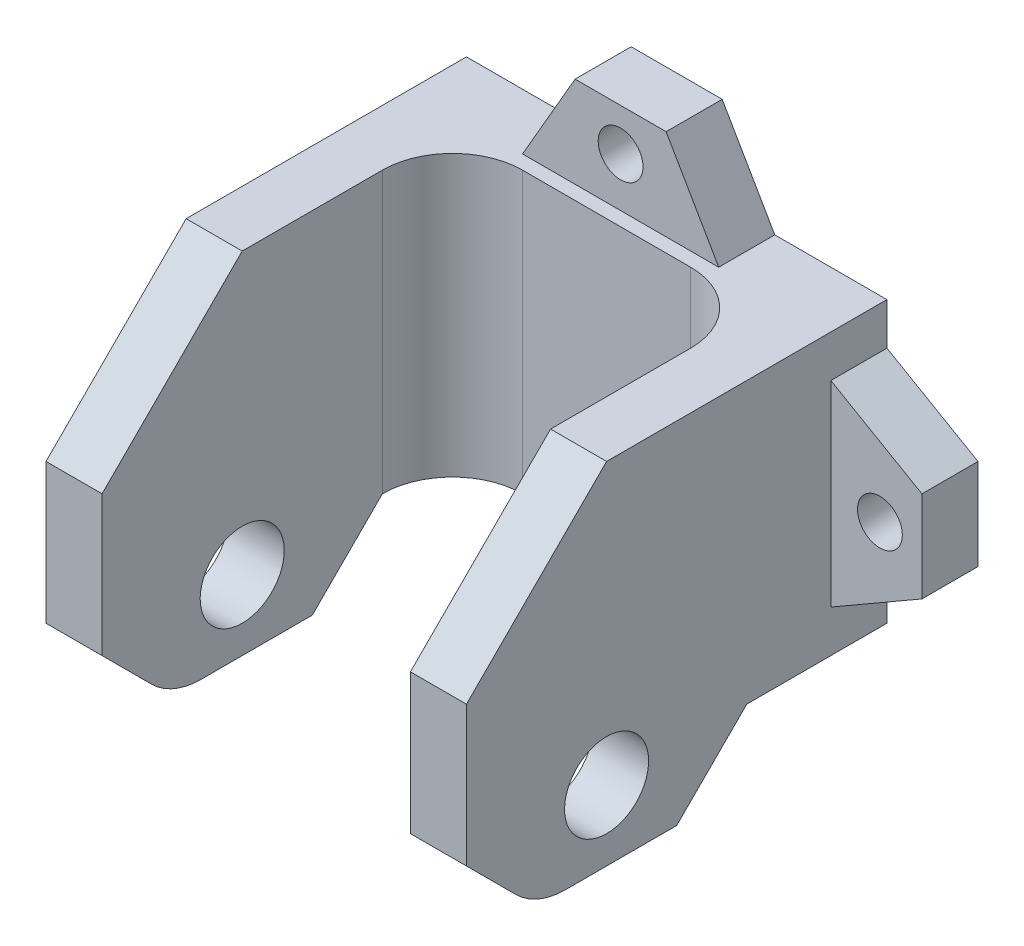
SolidWorks part; units mm, degrees
ref_plane "前视基准面" through (0, 0, 0) normal (0, 0, 1) x (1, 0, 0)
ref_plane "上视基准面" through (0, 0, 0) normal (0, 1, 0) x (1, 0, 0)
ref_plane "右视基准面" through (0, 0, 0) normal (1, 0, 0) x (0, 0, -1)
sketch "Sketch1" plane through (0, 0, 0) normal (0, 0, 1) x (1, 0, 0)
  line L0 (0, 285) -> (0, -299.6017) construction
  line L1 (-15, -45) -> (15, -45)
  line L2 (-15, -45) -> (-15, -85)
  line L3 (-15, -85) -> (15, -85)
  line L4 (15, -45) -> (15, -85)
  line L5 (225, 285) -> (-225, 285) construction
  line L6 (-115, -285) -> (115, -285) construction
  point P9 (0, -45)
  dimension "D1" = 30
  dimension "D2" = 40
  dimension "D3" = 200
extrude "Boss-Extrude1" add sketch "Sketch1" along normal blind 5
sketch "Sketch2" plane through (0, 0, 5) normal (0, 0, 1) x (1, 0, 0)
  line L0 (-15, -85) -> (15, -85) construction
  line L1 (-15, -45) -> (-11, -45)
  line L2 (-15, -45) -> (-15, -85)
  line L3 (-15, -85) -> (-11, -85)
  line L4 (-11, -45) -> (-11, -85)
  line L6 (15, -45) -> (11, -45)
  line L7 (15, -45) -> (15, -85)
  line L8 (15, -85) -> (11, -85)
  line L9 (11, -45) -> (11, -85)
  dimension "D1" = 4
  dimension "D2" = 4
extrude "Boss-Extrude2" add sketch "Sketch2" along normal blind 25
chamfer "Chamfer1" distance 10 angle 45 4 edges at (13, -85, 30) (-13, -85, 30) (13, -45, 30) (-13, -45, 30)
sketch "Sketch3" plane through (-15, 0, 0) normal (-1, 0, 0) x (0, 0, 1)
  line L0 (20, -45) -> (0, -45) construction
  line L1 (30, -55) -> (30, -75) construction
  circle A0 centre (20, -65) radius 3
  dimension "D1" = 20
  dimension "D2" = 6
  dimension "D3" = 10
extrude "Cut-Extrude1" cut sketch "Sketch3" against normal blind 76
sketch "Sketch4" plane through (-15, 0, 0) normal (-1, 0, 0) x (0, 0, 1)
  line L0 (30, -70) -> (15, -70)
  line L1 (30, -55) -> (30, -75) construction
  line L2 (15, -70) -> (10, -65)
  line L3 (10, -65) -> (0, -65)
  line L4 (0, -45) -> (0, -85) construction
  line L5 (30, -70) -> (31.2179, -87.2551)
  line L6 (31.2179, -87.2551) -> (-4.9062, -89.8049)
  line L7 (-4.9062, -89.8049) -> (0, -65)
  line L8 (20, -45) -> (5, -45) construction
  dimension "D1" = 25
  dimension "D2" = 5
  dimension "D3" = 45
  dimension "D4" = 10
extrude "Cut-Extrude2" cut sketch "Sketch4" against normal blind 76
chamfer "Chamfer2" distance 5 angle 45 2 edges at (-13, -70, 30) (13, -70, 30)
fillet "Fillet1" radius 5 2 edges at (11, -55, 5) (-11, -55, 5)
fillet "Fillet2" radius 5 2 edges at (13, -70, 25) (-13, -70, 25)
sketch "Sketch5" plane through (0, 0, 0) normal (0, 0, -1) x (-1, 0, 0)
  line L0 (7, -45) -> (3.2472, -38.5)
  line L1 (11, -45) -> (6, -45) construction
  line L2 (3.2472, -38.5) -> (-3.2472, -38.5)
  line L3 (-3.2472, -38.5) -> (-7, -45)
  line L4 (-6, -45) -> (-11, -45) construction
  line L5 (-7, -45) -> (7, -45)
  line L6 (15, -48) -> (21.5, -51.7528)
  line L7 (15, -55) -> (15, -45) construction
  line L8 (21.5, -51.7528) -> (21.5, -58.2472)
  line L9 (21.5, -58.2472) -> (15, -62)
  line L10 (15, -55) -> (15, -65) construction
  line L11 (15, -62) -> (15, -48)
  line L12 (0, -45) -> (0, -65) construction
  line L13 (-6, -65) -> (6, -65) construction
  line L14 (-15, -62) -> (-15, -48)
  line L15 (-21.5, -58.2472) -> (-15, -62)
  line L16 (-21.5, -51.7528) -> (-21.5, -58.2472)
  line L17 (-15, -48) -> (-21.5, -51.7528)
  line L18 (15, -45) -> (11, -45) construction
  circle A0 centre (0, -41.5) radius 1.6
  circle A1 centre (18.5, -55) radius 1.6
  circle A2 centre (-18.5, -55) radius 1.6
  point P32 (18.5, -54.5992)
  dimension "D6" = 3.2
  dimension "D7" = 3
  dimension "D8" = 3
  dimension "D1" = 60
  dimension "D2" = 6.5
  dimension "D3" = 7
  dimension "D4" = 7
  dimension "D5" = 3
  dimension "D9" = 7
  dimension "D10" = 7
extrude "Boss-Extrude3" add sketch "Sketch5" against normal blind 4 separate body
